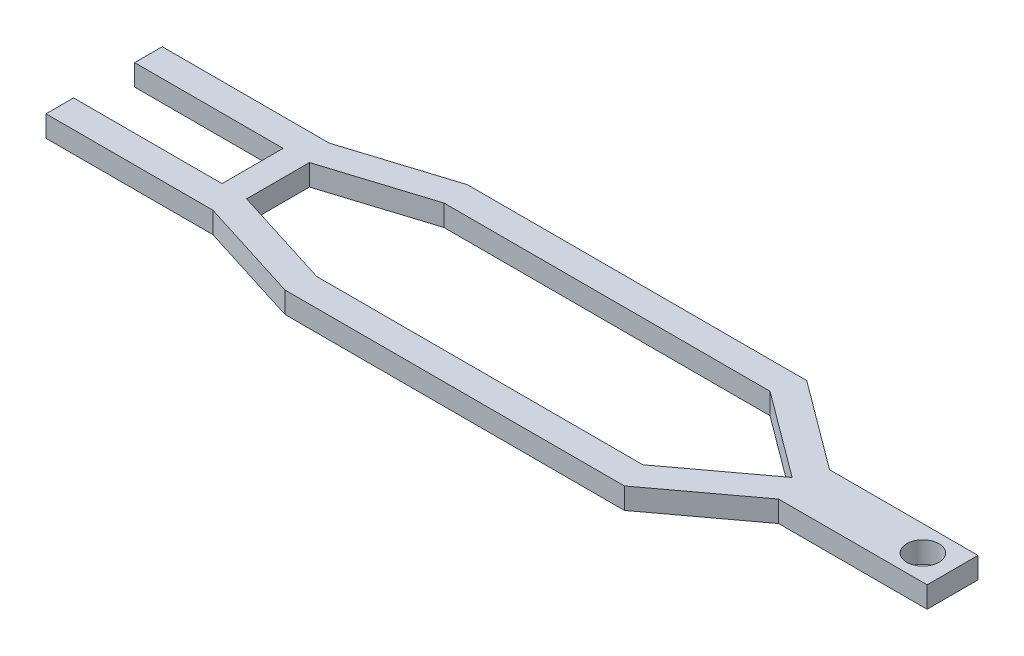
SolidWorks part; units mm, degrees
ref_plane "Front Plane" through (0, 0, 0) normal (0, 0, 1) x (1, 0, 0)
ref_plane "Top Plane" through (0, 0, 0) normal (0, 1, 0) x (1, 0, 0)
ref_plane "Right Plane" through (0, 0, 0) normal (1, 0, 0) x (0, 0, -1)
sketch "Sketch2" plane through (0, 0, 0) normal (0, 1, 0) x (1, 0, 0)
  line L0 (0, 0) -> (272.4392, 0) construction
  line L1 (0, -13.7) -> (39.3361, -13.7)
  line L2 (39.3361, -13.7) -> (64.1325, -21.5)
  line L3 (64.1325, -21.5) -> (144.1325, -21.5)
  line L4 (144.1325, -21.5) -> (165, -6)
  line L5 (165, -6) -> (200, -6)
  line L6 (200, -6) -> (200, 6)
  line L12 (0, -13.7) -> (0, -7.2)
  line L13 (0, -7.2) -> (35, -7.2)
  line L14 (35, -7.2) -> (35, 7.2)
  line L16 (0, 7.2) -> (35, 7.2)
  line L17 (0, 13.7) -> (0, 7.2)
  line L21 (165, 6) -> (200, 6)
  line L22 (144.1325, 21.5) -> (165, 6)
  line L23 (64.1325, 21.5) -> (144.1325, 21.5)
  line L24 (39.3361, 13.7) -> (64.1325, 21.5)
  line L25 (0, 13.7) -> (39.3361, 13.7)
  dimension "D2" = 43
  dimension "D3" = 200
  dimension "D4" = 6.5
  dimension "D5" = 80
  dimension "D6" = 7.2
  dimension "D9" = 35
  dimension "D10" = 35
  dimension "D12" = 39.3361
  dimension "D13" = 12
extrude "Boss-Extrude1" add sketch "Sketch2" along normal blind 5
sketch "Sketch3" plane through (0, 5, 0) normal (0, 1, 0) x (1, 0, 0)
  line L2 (64.1325, 21.5) -> (39.3361, 13.7) construction
  line L3 (35, 7.2) -> (35, -7.2) construction
  line L4 (144.1325, -21.5) -> (165, -6) construction
  line L5 (200, -6) -> (200, 6) construction
  line L6 (200, 6) -> (165, 6) construction
  line L30 (41, 7.4094) -> (41, -7.4094)
  line L31 (41, -7.4094) -> (65.1307, -15)
  line L32 (65.1307, -15) -> (141.9826, -15)
  line L33 (141.9826, -15) -> (162.1769, 0)
  line L35 (162.1769, 0) -> (141.9826, 15)
  line L36 (141.9826, 15) -> (65.1307, 15)
  line L37 (65.1307, 15) -> (41, 7.4094)
  line L38 (144.1325, 21.5) -> (64.1325, 21.5) construction
  line L39 (64.1325, -21.5) -> (144.1325, -21.5) construction
  line L40 (104.1325, 21.5) -> (104.1325, -21.5) construction
  line L41 (165, 6) -> (144.1325, 21.5) construction
  circle A0 centre (193, 0) radius 3.8
  point P21 (200, 0)
  point P29 (51.7343, 17.6)
  dimension "D6" = 7.6
  dimension "D1" = 6.5
  dimension "D2" = 6.5
  dimension "D3" = 6
  dimension "D4" = 6.5
  dimension "D5" = 6.5
  dimension "D7" = 7
  dimension "D8" = 6
extrude "Cut-Extrude1" cut sketch "Sketch3" against normal through all
